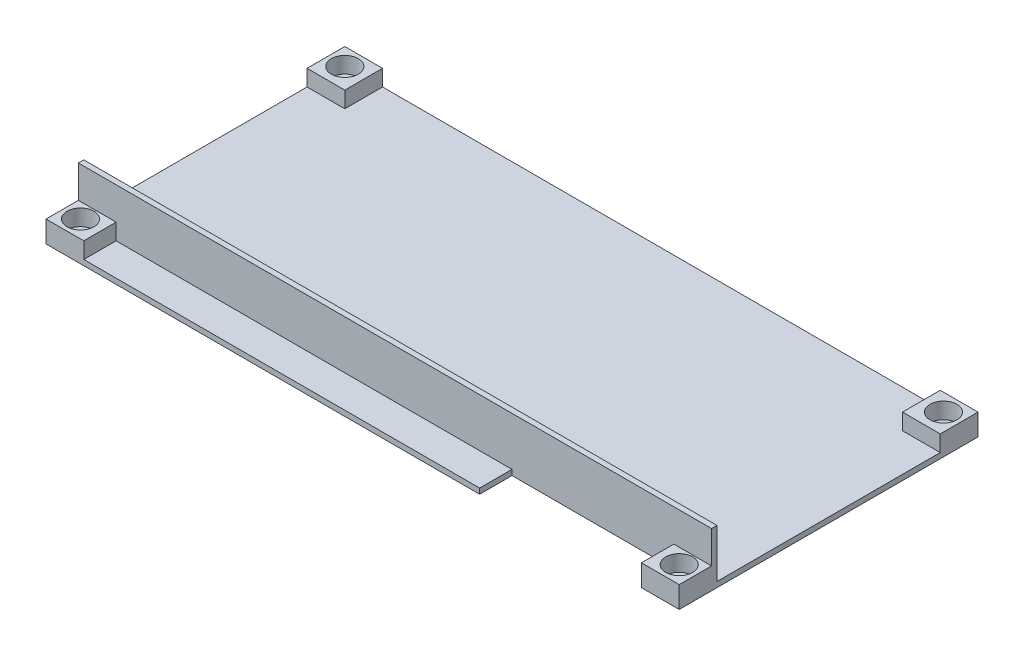
SolidWorks part; units mm, degrees
ref_plane "Front Plane" through (0, 0, 0) normal (0, 0, 1) x (1, 0, 0)
ref_plane "Top Plane" through (0, 0, 0) normal (0, 1, 0) x (1, 0, 0)
ref_plane "Right Plane" through (0, 0, 0) normal (1, 0, 0) x (0, 0, -1)
sketch "Sketch1" plane through (0, 0, 0) normal (0, 1, 0) x (1, 0, 0)
  line L1 (-58.7, -27.7) -> (58.7, -27.7)
  line L2 (-58.7, -27.7) -> (-58.7, 27.7)
  line L3 (-58.7, 27.7) -> (58.7, 27.7)
  line L4 (58.7, -27.7) -> (58.7, 27.7)
  line L5 (-58.7, -27.7) -> (58.7, 27.7) construction
  line L6 (-58.7, 27.7) -> (58.7, -27.7) construction
  point P0 (0, 0)
  dimension "D1" = 55.4
  dimension "D2" = 117.4
extrude "Boss-Extrude1" add sketch "Sketch1" along normal blind 1
sketch "Sketch2" plane through (0, 1, 0) normal (0, 1, 0) x (1, 0, 0)
  line L0 (0, 27.7) -> (0, -27.7) construction
  line L1 (58.7, 27.7) -> (-58.7, 27.7) construction
  line L2 (-58.7, -27.7) -> (58.7, -27.7) construction
  line L3 (-58.7, 0) -> (58.7, 0) construction
  line L4 (-58.7, 27.7) -> (-58.7, -27.7) construction
  line L5 (58.7, -27.7) -> (58.7, 27.7) construction
  line L6 (58.7, 20.7) -> (51.7, 20.7)
  line L7 (-58.7, 27.7) -> (-51.7, 27.7)
  line L8 (-58.7, 27.7) -> (-58.7, 20.7)
  line L9 (-58.7, 20.7) -> (-51.7, 20.7)
  line L10 (-51.7, 27.7) -> (-51.7, 20.7)
  line L11 (51.7, 27.7) -> (51.7, 20.7)
  line L12 (58.7, 27.7) -> (51.7, 27.7)
  line L13 (58.7, 27.7) -> (58.7, 20.7)
  line L14 (58.7, -27.7) -> (58.7, -20.7)
  line L15 (58.7, -27.7) -> (51.7, -27.7)
  line L16 (51.7, -27.7) -> (51.7, -20.7)
  line L17 (58.7, -20.7) -> (51.7, -20.7)
  line L18 (-58.7, -20.7) -> (-51.7, -20.7)
  line L19 (-51.7, -27.7) -> (-51.7, -20.7)
  line L20 (-58.7, -27.7) -> (-51.7, -27.7)
  line L21 (-58.7, -27.7) -> (-58.7, -20.7)
  dimension "D1" = 7
extrude "Boss-Extrude2" add sketch "Sketch2" along normal blind 3
sketch "Sketch3" plane through (0, 4, 0) normal (0, 1, 0) x (1, 0, 0)
  line L1 (-55.5, -24.5) -> (55.5, -24.5) construction
  line L2 (-55.5, -24.5) -> (-55.5, 24.5) construction
  line L3 (-55.5, 24.5) -> (55.5, 24.5) construction
  line L4 (55.5, -24.5) -> (55.5, 24.5) construction
  line L5 (-55.5, -24.5) -> (55.5, 24.5) construction
  line L6 (-55.5, 24.5) -> (55.5, -24.5) construction
  circle A0 centre (-55.5, 24.5) radius 1.35
  circle A1 centre (55.5, 24.5) radius 1.35
  circle A2 centre (55.5, -24.5) radius 1.35
  circle A3 centre (-55.5, -24.5) radius 1.35
  point P0 (0, 0)
  dimension "D3" = 2.7
  dimension "D1" = 49
  dimension "D2" = 111
extrude "Cut-Extrude1" cut sketch "Sketch3" against normal through all
sketch "Sketch7" plane through (0, 0, 0) normal (0, -1, 0) x (1, 0, 0)
  line L1 (51.7, 27.7) -> (21.7, 27.7)
  line L2 (51.7, 27.7) -> (51.7, 21.7)
  line L3 (51.7, 21.7) -> (21.7, 21.7)
  line L4 (21.7, 27.7) -> (21.7, 21.7)
  dimension "D1" = 30
  dimension "D2" = 6
extrude "Cut-Extrude5" cut sketch "Sketch7" against normal through all
sketch "Sketch9" plane through (0, 4, 0) normal (0, 1, 0) x (1, 0, 0)
  circle A0 centre (-55.5, 24.5) radius 2.5
  circle A1 centre (55.5, 24.5) radius 2.5
  circle A2 centre (55.5, -24.5) radius 2.5
  circle A3 centre (-55.5, -24.5) radius 2.5
  dimension "D1" = 5
extrude "Cut-Extrude6" cut sketch "Sketch9" against normal offset from surface (3 mm away) 1 up to face at (18.35, 0, 12.35)
sketch "Sketch10" plane through (0, 1, 0) normal (0, 1, 0) x (1, 0, 0)
  line L0 (58.7, -20.7) -> (58.7, 20.7) construction
  line L1 (58.7, -21.7) -> (-58.7, -21.7)
  line L2 (58.7, -21.7) -> (58.7, -20.7)
  line L3 (58.7, -20.7) -> (-58.7, -20.7)
  line L4 (-58.7, -21.7) -> (-58.7, -20.7)
  line L5 (-58.7, 20.7) -> (-58.7, -20.7) construction
  line L7 (-51.7, -27.7) -> (21.7, -27.7) construction
  dimension "D1" = 1
  dimension "D2" = 6
extrude "Boss-Extrude3" add sketch "Sketch10" along normal blind 9
